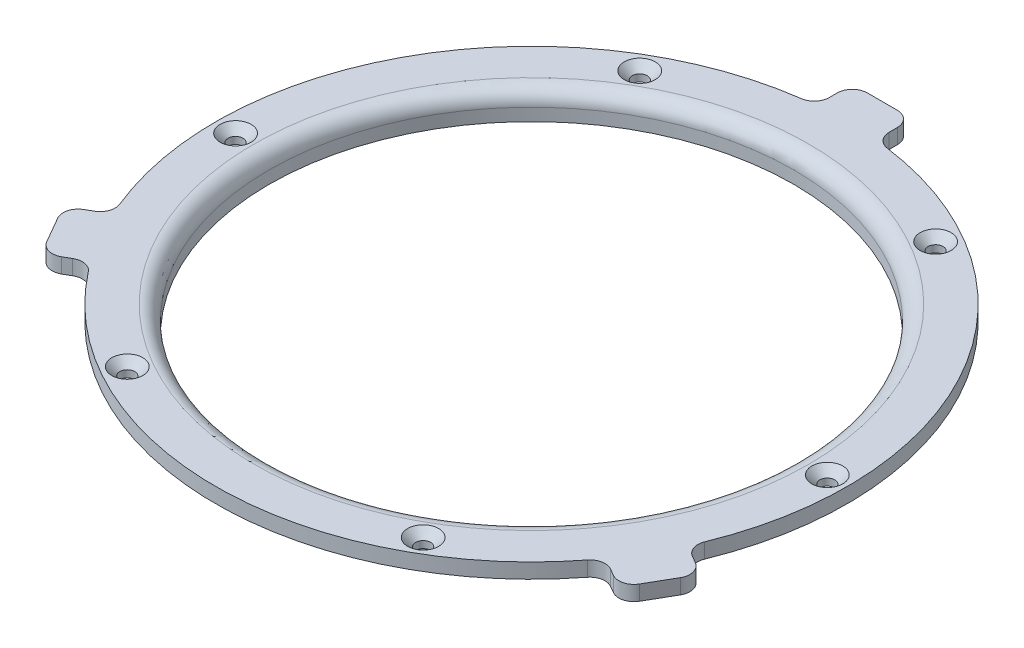
SolidWorks part; units mm, degrees
material "PET"
ref_plane "Front Plane" through (0, 0, 0) normal (0, 0, 1) x (1, 0, 0)
ref_plane "Top Plane" through (0, 0, 0) normal (0, 1, 0) x (1, 0, 0)
ref_plane "Right Plane" through (0, 0, 0) normal (1, 0, 0) x (0, 0, -1)
sketch "Sketch2" plane through (0, 0, 0) normal (0, 0, 1) x (1, 0, 0)
  line L0 (-55, 9.3) -> (-52.5, 9.3)
  line L1 (-52.5, 9.3) -> (-52.5, 14.8)
  line L2 (-52.5, 14.8) -> (-63.2, 14.8)
  line L3 (-63.2, 14.8) -> (-63.2, 11.8)
  line L4 (-63.2, 11.8) -> (-55, 11.8)
  line L5 (-55, 11.8) -> (-55, 9.3)
  line L11 (0, 0) -> (0, 30.013) construction
sketch "Sketch3" plane through (0, 0, 0) normal (0, 0, 1) x (1, 0, 0)
  line L6 (-55, 9.3) -> (-52.5, 9.3)
  line L7 (-52.5, 9.3) -> (-52.5, 14.8)
  line L8 (-52.5, 14.8) -> (-63.2, 14.8)
  line L9 (-63.2, 14.8) -> (-63.2, 11.8)
  line L10 (-63.2, 11.8) -> (-55, 11.8)
  line L11 (-55, 11.8) -> (-55, 9.3)
  line L12 (-55, 9.3) -> (-52.5, 9.3)
  line L13 (-52.5, 9.3) -> (-52.5, 14.8)
  line L14 (-52.5, 14.8) -> (-63.2, 14.8)
  line L15 (-63.2, 14.8) -> (-63.2, 11.8)
  line L16 (-63.2, 11.8) -> (-55, 11.8)
  line L17 (-55, 11.8) -> (-55, 9.3)
  dimension "D1" = 0
revolve "Cap" add sketch "Sketch3" angle 360 about L11
sketch "Sketch9" plane through (0, 0, 0) normal (0, 0, 1) x (1, 0, 0)
  line L0 (-63.2, 11.8) -> (-55.2, 11.8) construction
  line L4 (-59.2, 11.8) -> (-59.2, -3.2)
  line L5 (-59.2, 11.8) -> (-57.7, 11.8)
  line L6 (-59.2, 11.8) -> (-57.1, 11.8)
  point P3 (-59.2, 11.8)
  point P8 (0, 0)
  point P10 (0, 0)
sketch "Sketch10" plane through (0, 0, 0) normal (0, 1, 0) x (1, 0, 0)
  circle A0 centre (-59.2, 0) radius 2.1
  point P0 (-59.2, 0)
  point P1 (-57.1, 0)
hole_wizard "CSK for M3 Flat Head Machine Screw1" positions "Sketch11" profile "Sketch12" countersink size "M3" standard "ANSI Metric"
sketch "Sketch11" plane through (0, 14.8, 0) normal (0, 1, 0) x (1, 0, 0)
  point P0 (-59.2, 0)
sketch "Sketch12" plane through (-59.2, 14.8, 0) normal (1, 0, 0) x (0, 0, 1)
  line L0 (0, 0) -> (0, 9.7913)
  line L1 (0, 9.7913) -> (1.5, 8.89)
  line L2 (1.5, 8.89) -> (1.5, 1.6)
  line L3 (1.5, 1.6) -> (3.1, 0)
  line L5 (3.1, 0) -> (0, 0)
  line L6 (-1.5, 1.6) -> (-3.1, 0) construction
  line L10 (0, 9.7913) -> (-1.5, 8.89) construction
  line L11 (0, -6.35) -> (0, 107.95) construction
  dimension "Hole Dia." = 3
  dimension "Hole Depth" = 8.89
  dimension "Near C'Sink Dia." = 6.2
  dimension "Near C'Sink Angle" = 90
  dimension "Drill Angle" = 118
pattern_circular "CirPattern1" count 6 over 360 about axis through (0, 0, 0) along (0, 1, 0) of "CSK for M3 Flat Head Machine Screw1"
fillet "Fillet1" radius 3 1 edges at (52.5, 14.8, 0)
sketch "Sketch13" plane through (0, 0, 0) normal (0, 0, 1) x (1, 0, 0)
  line L0 (-63.4027, 9.8) -> (-70.2, 9.8)
  line L2 (-70.2, 9.8) -> (-70.2, -3.2)
  line L3 (-70.2, -3.2) -> (-63.4027, -3.2)
  line L4 (-63.4027, -3.2) -> (-63.4027, 9.8)
  line L6 (0, 0) -> (0, 30.013) construction
sketch "Sketch14" plane through (0, 0, 0) normal (0, 1, 0) x (1, 0, 0)
  line L0 (-70.2, 0) -> (-63.4027, 0) construction
  line L1 (-70.2, 0) -> (-63.4027, 0) construction
  line L2 (-63.4027, 0) -> (-70.2, 0) construction
  line L3 (-63.795, -29.9038) -> (-57.795, -40.2962)
  line L4 (-63.795, -29.9038) -> (-57.4856, -26.2611)
  line L5 (-57.795, -40.2962) -> (-51.4856, -36.6534)
  line L6 (-57.4856, -26.2611) -> (-51.4856, -36.6534)
  point P5 (-60.795, -35.1)
  dimension "D1" = 12
extrude "Boss-Extrude1" add sketch "Sketch14" against normal up to surface (3 mm away) from surface at 14.8 up to face at (-31.1, 11.8, 51.2687) starting at face at (55.5, 14.8, 0)
fillet "Fillet2" radius 3 4 edges at (-57.4856, 13.3, 26.2611) (-63.795, 13.3, 29.9038) (-57.795, 13.3, 40.2962) (-51.4856, 13.3, 36.6534)
pattern_circular "CirPattern2" count 3 over 360 about axis through (0, 0, 0) along (0, 1, 0) of "Boss-Extrude1", "Fillet2"
equation "\"TopHoles\"= 6"
equation "\"D1@CirPattern1\"=\"TopHoles\""
